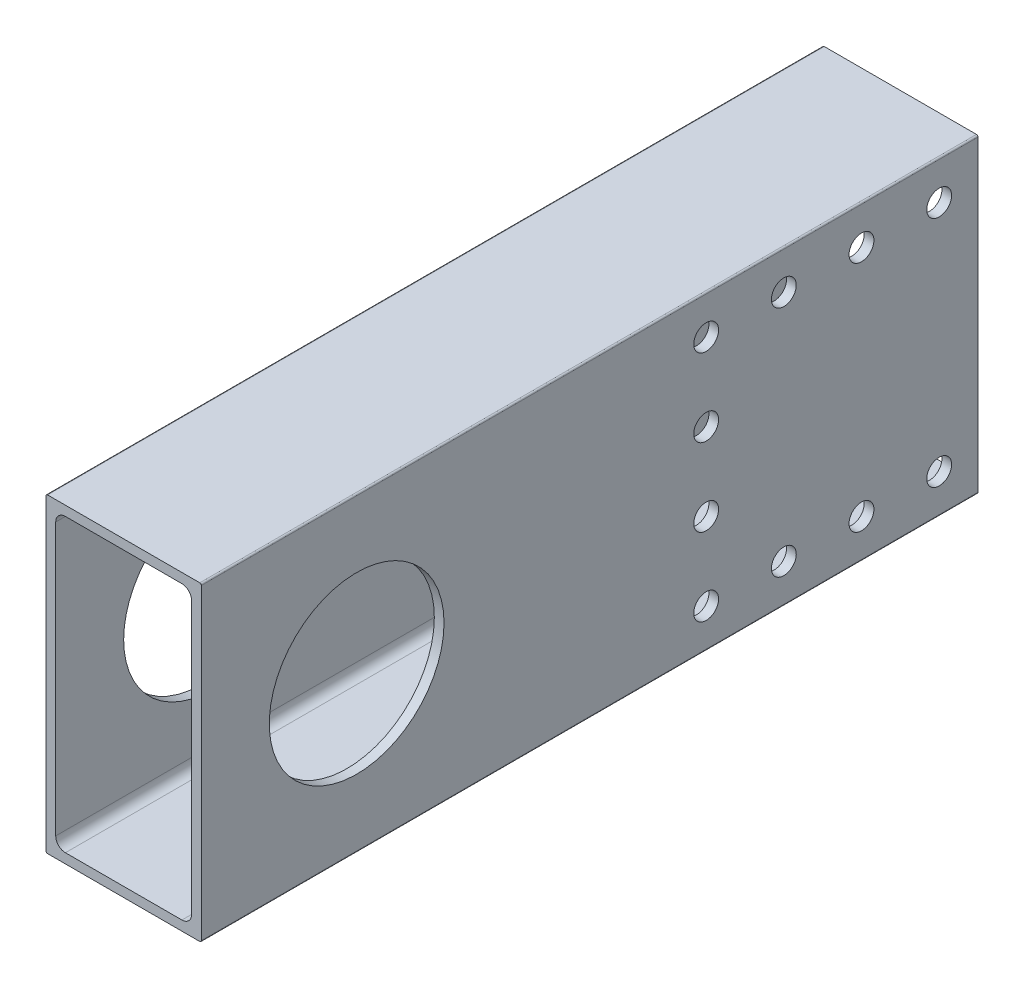
SolidWorks part; units mm, degrees
material "1060 Alloy"
ref_plane "Front Plane" through (0, 0, 0) normal (0, 0, 1) x (1, 0, 0)
ref_plane "Top Plane" through (0, 0, 0) normal (0, 1, 0) x (1, 0, 0)
ref_plane "Right Plane" through (0, 0, 0) normal (1, 0, 0) x (0, 0, -1)
ref_plane "Plane1" through (0, 0, 0) normal (0, 0, -1) x (-1, 0, 0)
sketch "Sketch1" plane through (0, 0, 0) normal (0, 0, -1) x (-1, 0, 0)
  line L0 (-11.1125, -22.225) -> (-11.1125, 22.225)
  line L1 (-9.525, 23.8125) -> (9.525, 23.8125)
  line L2 (11.1125, 22.225) -> (11.1125, -22.225)
  line L3 (9.525, -23.8125) -> (-9.525, -23.8125)
  line L4 (-12.7, 25.146) -> (-12.7, -25.146)
  line L5 (-12.446, -25.4) -> (12.446, -25.4)
  line L6 (12.7, -25.146) -> (12.7, 25.146)
  line L7 (12.446, 25.4) -> (-12.446, 25.4)
  arc A0 (-11.1125, 22.225) -> (-9.525, 23.8125) centre (-9.525, 22.225) cw
  arc A1 (9.525, 23.8125) -> (11.1125, 22.225) centre (9.525, 22.225) cw
  arc A2 (11.1125, -22.225) -> (9.525, -23.8125) centre (9.525, -22.225) cw
  arc A3 (-9.525, -23.8125) -> (-11.1125, -22.225) centre (-9.525, -22.225) cw
  arc A4 (-12.7, -25.146) -> (-12.446, -25.4) centre (-12.446, -25.146) ccw
  arc A5 (12.446, -25.4) -> (12.7, -25.146) centre (12.446, -25.146) ccw
  arc A6 (12.7, 25.146) -> (12.446, 25.4) centre (12.446, 25.146) ccw
  arc A7 (-12.446, 25.4) -> (-12.7, 25.146) centre (-12.446, 25.146) ccw
extrude "Boss-Extrude1" add sketch "Sketch1" against normal blind 127
sketch "Sketch2" plane through (12.7, 0, 0) normal (1, 0, 0) x (0, 0, -1)
  line L0 (-127, 0) -> (-101.6, 0) construction
  line L1 (-127, 25.146) -> (-127, -25.146) construction
  circle A0 centre (-101.6, 0) radius 14.2875
  dimension "D1" = 28.575
  dimension "D2" = 25.4
extrude "Cut-Extrude1" cut sketch "Sketch2" against normal blind 25.4
sketch "Sketch3" plane through (12.7, 0, 0) normal (1, 0, 0) x (0, 0, -1)
  circle A0 centre (-44.45, -19.05) radius 2.032
  circle A1 centre (-44.45, -6.35) radius 2.032
  circle A2 centre (-44.45, 19.05) radius 2.032
  circle A4 centre (-31.75, 19.05) radius 2.032
  circle A5 centre (-19.05, 19.05) radius 2.032
  circle A6 centre (-6.35, 19.05) radius 2.032
  circle A7 centre (-44.45, 6.35) radius 2.032
  circle A8 centre (-31.75, -19.05) radius 2.032
  circle A9 centre (-19.05, -19.05) radius 2.032
  circle A10 centre (-6.35, -19.05) radius 2.032
extrude "Cut-Extrude2" cut sketch "Sketch3" against normal through all both
